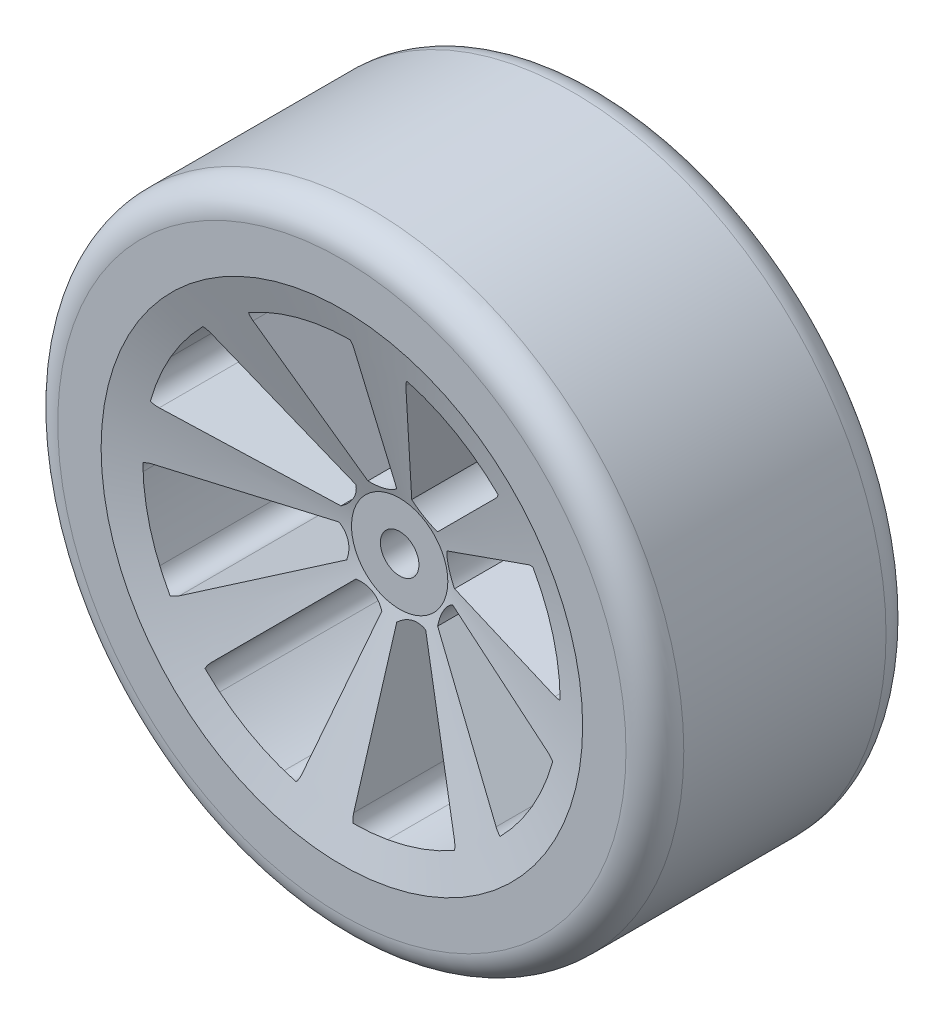
SolidWorks part; units mm, degrees
ref_plane "Front" through (0, 0, 0) normal (0, 0, 1) x (1, 0, 0)
ref_plane "Top" through (0, 0, 0) normal (0, 1, 0) x (1, 0, 0)
ref_plane "Right" through (0, 0, 0) normal (1, 0, 0) x (0, 0, -1)
sketch "草图1" plane through (0, 0, 0) normal (0, 0, 1) x (1, 0, 0)
  circle A0 centre (0, 0) radius 32.5
extrude "凸台-拉伸1" add sketch "草图1" along normal blind 27
fillet "圆角1" radius 3 2 edges at (32.5, 0, 27) (32.5, 0, 0)
sketch "草图4" plane through (0, 0, 0) normal (0, 1, 0) x (1, 0, 0)
  line L0 (0, -27) -> (0, -21)
  line L1 (-29.5, -27) -> (29.5, -27) construction
  line L2 (0, -21) -> (5, -21)
  line L3 (0, -27) -> (25, -27)
  line L4 (5, -21) -> (25, -27)
  line L5 (0, -6) -> (0, 0)
  line L6 (0, 0) -> (25, 0)
  line L7 (25, 0) -> (5, -6)
  line L9 (0, -6) -> (5, -6)
  point P12 (6, -5.4498)
revolve "切除-旋转1" cut sketch "草图4" angle 360 about L0
sketch "草图5" plane through (0, 0, 21) normal (0, 0, 1) x (1, 0, 0)
  circle A0 centre (0, 0) radius 2
extrude "切除-拉伸1" cut sketch "草图5" against normal blind 15 contours A0
sketch "草图6" plane through (0, 0, 0) normal (0, 0, -1) x (-1, 0, 0)
  line L0 (6, 0) -> (20.9045, 0)
  line L1 (5.1962, -3) -> (18.1039, -10.4523)
  line L2 (1.5529, -5.7956) -> (5.4105, -20.1922)
  line L3 (4.2426, -4.2426) -> (14.7817, -14.7817)
  line L4 (-3, -5.1962) -> (-10.4523, -18.1039)
  line L5 (0, -6) -> (0, -20.9045)
  line L6 (-5.7956, -1.5529) -> (-20.1922, -5.4105)
  line L7 (-4.2426, -4.2426) -> (-14.7817, -14.7817)
  line L8 (-5.1962, 3) -> (-18.1039, 10.4523)
  line L9 (-6, 0) -> (-20.9045, 0)
  line L10 (-1.5529, 5.7956) -> (-5.4105, 20.1922)
  line L11 (-4.2426, 4.2426) -> (-14.7817, 14.7817)
  line L12 (3, 5.1962) -> (10.4523, 18.1039)
  line L13 (0, 6) -> (0, 20.9045)
  line L14 (5.7956, 1.5529) -> (20.1922, 5.4105)
  line L15 (4.2426, 4.2426) -> (14.7817, 14.7817)
  arc A2 (20.9233, -9.5507) -> (22.8955, -2.1905) centre (0, 0) ccw
  arc A3 (6, 0) -> (5.1962, -3) centre (8.393, -2.2489) ccw
  arc A4 (8.0416, -21.5484) -> (14.6406, -17.7384) centre (0, 0) ccw
  arc A5 (4.2426, -4.2426) -> (1.5529, -5.7956) centre (4.3445, -7.5249) ccw
  arc A6 (-9.5507, -20.9233) -> (-2.1905, -22.8955) centre (0, 0) ccw
  arc A7 (0, -6) -> (-3, -5.1962) centre (-2.2489, -8.393) ccw
  arc A8 (-21.5484, -8.0416) -> (-17.7384, -14.6406) centre (0, 0) ccw
  arc A9 (-4.2426, -4.2426) -> (-5.7956, -1.5529) centre (-7.5249, -4.3445) ccw
  arc A10 (-20.9233, 9.5507) -> (-22.8955, 2.1905) centre (0, 0) ccw
  arc A11 (-6, 0) -> (-5.1962, 3) centre (-8.393, 2.2489) ccw
  arc A12 (-8.0416, 21.5484) -> (-14.6406, 17.7384) centre (0, 0) ccw
  arc A13 (-4.2426, 4.2426) -> (-1.5529, 5.7956) centre (-4.3445, 7.5249) ccw
  arc A14 (9.5507, 20.9233) -> (2.1905, 22.8955) centre (0, 0) ccw
  arc A15 (0, 6) -> (3, 5.1962) centre (2.2489, 8.393) ccw
  arc A16 (21.5484, 8.0416) -> (17.7384, 14.6406) centre (0, 0) ccw
  arc A17 (4.2426, 4.2426) -> (5.7956, 1.5529) centre (7.5249, 4.3445) ccw
  arc A18 (20.1922, 5.4105) -> (21.5484, 8.0416) centre (19.6746, 7.3423) ccw
  arc A19 (14.7817, 14.7817) -> (17.7384, 14.6406) centre (16.196, 13.3675) cw
  arc A20 (20.9045, 0) -> (22.8955, -2.1905) centre (20.9045, -2) cw
  arc A21 (18.1039, -10.4523) -> (20.9233, -9.5507) centre (19.1039, -8.7202) ccw
  arc A22 (14.7817, -14.7817) -> (14.6406, -17.7384) centre (13.3675, -16.196) cw
  arc A23 (8.0416, -21.5484) -> (5.4105, -20.1922) centre (7.3423, -19.6746) cw
  arc A24 (-2.1905, -22.8955) -> (0, -20.9045) centre (-2, -20.9045) ccw
  arc A25 (-10.4523, -18.1039) -> (-9.5507, -20.9233) centre (-8.7202, -19.1039) ccw
  arc A26 (-17.7384, -14.6406) -> (-14.7817, -14.7817) centre (-16.196, -13.3675) ccw
  arc A27 (-21.5484, -8.0416) -> (-20.1922, -5.4105) centre (-19.6746, -7.3423) cw
  arc A28 (-22.8955, 2.1905) -> (-20.9045, 0) centre (-20.9045, 2) ccw
  arc A29 (-20.9233, 9.5507) -> (-18.1039, 10.4523) centre (-19.1039, 8.7202) cw
  arc A30 (-14.6406, 17.7384) -> (-14.7817, 14.7817) centre (-13.3675, 16.196) ccw
  arc A31 (-8.0416, 21.5484) -> (-5.4105, 20.1922) centre (-7.3423, 19.6746) cw
  arc A32 (2.1905, 22.8955) -> (0, 20.9045) centre (2, 20.9045) ccw
  arc A33 (9.5507, 20.9233) -> (10.4523, 18.1039) centre (8.7202, 19.1039) cw
  point P44 (0, 0)
  dimension "D1" = 8
  dimension "D2" = 2
  dimension "D3" = 2
  dimension "D4" = 2
  dimension "D5" = 2
  dimension "D6" = 2
  dimension "D7" = 2
  dimension "D8" = 2
  dimension "D9" = 2
  dimension "D10" = 2
  dimension "D11" = 2
  dimension "D12" = 2
  dimension "D13" = 2
  dimension "D14" = 2
  dimension "D15" = 2
  dimension "D16" = 2
  dimension "D17" = 2
extrude "切除-拉伸2" cut sketch "草图6" against normal blind 26
